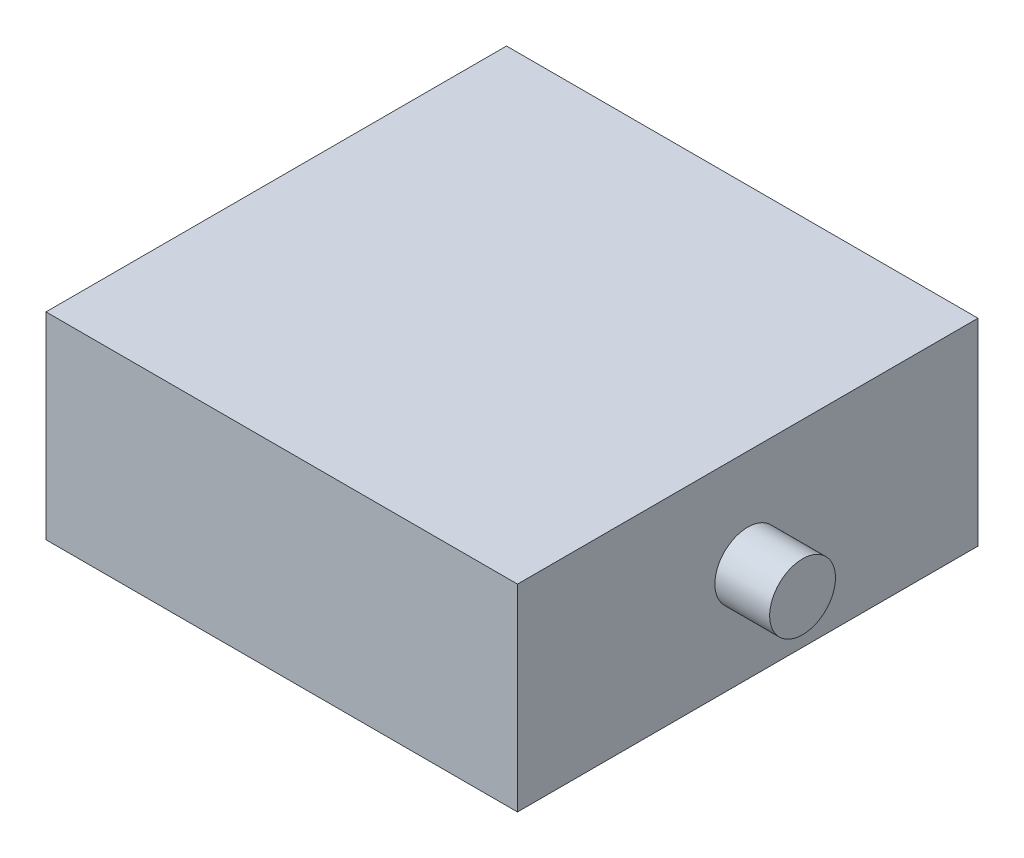
SolidWorks part; units mm, degrees
ref_plane "Front Plane" through (0, 0, 0) normal (0, 0, 1) x (1, 0, 0)
ref_plane "Top Plane" through (0, 0, 0) normal (0, 1, 0) x (1, 0, 0)
ref_plane "Right Plane" through (0, 0, 0) normal (1, 0, 0) x (0, 0, -1)
sketch "Sketch2" plane through (0, 0, 0) normal (0, 1, 0) x (1, 0, 0)
  line L0 (0, 0) -> (48, 0)
  line L1 (48, 0) -> (48, 42)
  line L2 (48, 42) -> (0, 42)
  line L3 (0, 42) -> (0, 0)
  dimension "D1" = 48
  dimension "D2" = 42
extrude "Boss-Extrude1" add sketch "Sketch2" along normal blind 18
sketch "Sketch3" plane through (48, 0, 0) normal (1, 0, 0) x (0, 0, -1)
  line L0 (0, 18) -> (42, 18) construction
  line L2 (0, 18) -> (42, 18)
  line L3 (0, 18) -> (0, 0)
  line L4 (0, 0) -> (42, 0)
  line L5 (42, 18) -> (42, 0)
  circle A0 centre (21, 9) radius 3
  point P4 (21, 18)
  point P11 (0, 0)
  point P12 (0, 9)
  dimension "D2" = 6
  dimension "D1" = 0
extrude "Cut-Extrude1" cut sketch "Sketch3" against normal blind 5 contours L3 L2 L5 L4 | A0
